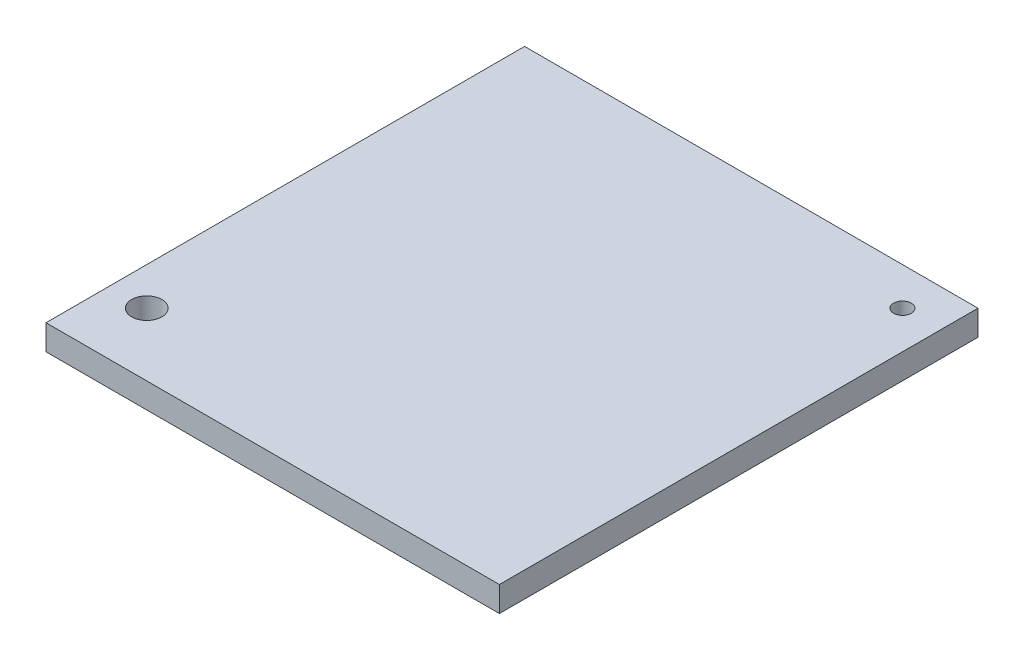
SolidWorks part; units mm, degrees
material "GE-223 Carbon Based Ablator"
ref_plane "Front Plane" through (0, 0, 0) normal (0, 0, 1) x (1, 0, 0)
ref_plane "Top Plane" through (0, 0, 0) normal (0, 1, 0) x (1, 0, 0)
ref_plane "Right Plane" through (0, 0, 0) normal (1, 0, 0) x (0, 0, -1)
sketch "Sketch1" plane through (0, 0, 0) normal (0, 1, 0) x (1, 0, 0)
  line L1 (-90, 90) -> (90, 90)
  line L2 (-90, 90) -> (-90, -100)
  line L3 (-90, -100) -> (90, -100)
  line L4 (90, 90) -> (90, -100)
  dimension "D1" = 190
  dimension "D2" = 180
  dimension "D3" = 90
  dimension "D4" = 90
extrude "Boss-Extrude1" add sketch "Sketch1" along normal blind 10
sketch "Sketch2" plane through (0, 10, 0) normal (0, 1, 0) x (1, 0, 0)
  line L0 (90, -100) -> (90, 90) construction
  line L1 (90, 90) -> (-90, 90) construction
  line L2 (-90, 90) -> (-90, -100) construction
  line L3 (-90, -100) -> (90, -100) construction
  circle A0 centre (75, 75) radius 3.5
  circle A1 centre (-75, -85) radius 6
  dimension "D1" = 7
  dimension "D4" = 12
  dimension "D2" = 15
  dimension "D3" = 15
  dimension "D5" = 15
  dimension "D6" = 15
extrude "Cut-Extrude1" cut sketch "Sketch2" against normal through all contours A0
sketch "Sketch6" plane through (0, 10, 0) normal (0, 1, 0) x (1, 0, 0)
  line L0 (-90, -100) -> (90, -100) construction
  line L1 (-90, 90) -> (-90, -100) construction
  circle A0 centre (-75, -75) radius 6
  dimension "D1" = 12
  dimension "D2" = 25
  dimension "D3" = 15
extrude "Cut-Extrude2" cut sketch "Sketch6" against normal through all contours A0
